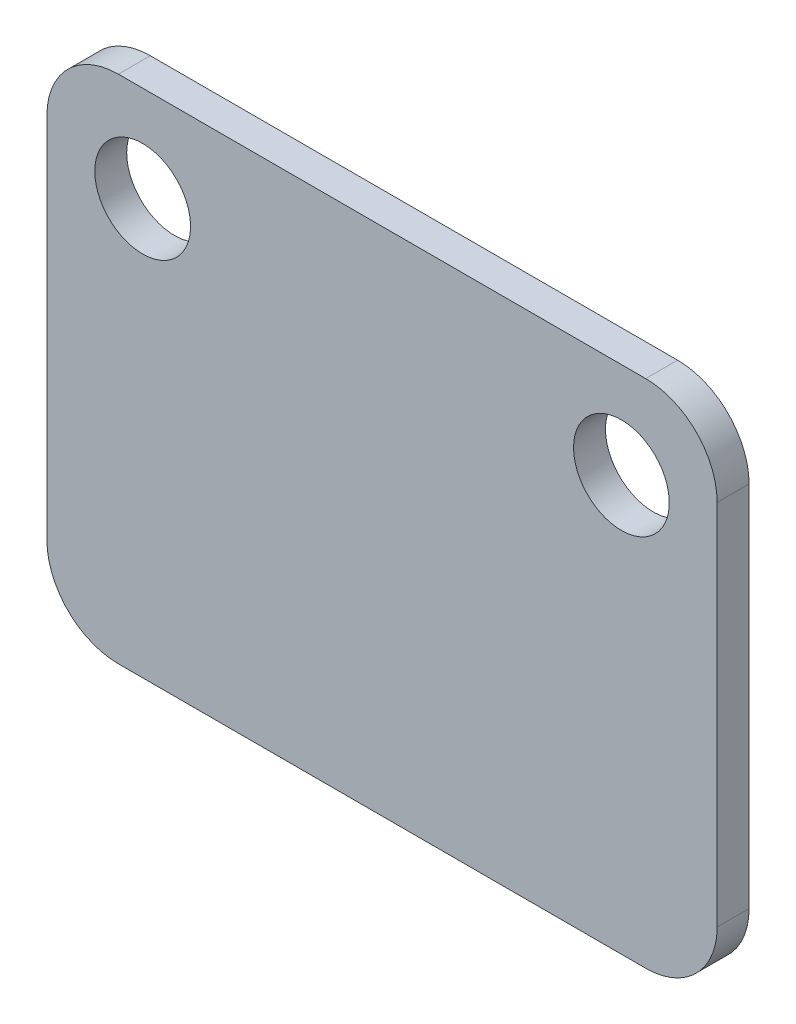
SolidWorks part; units mm, degrees
material "Cobre"
ref_plane "Plano frontal" through (0, 0, 0) normal (0, 0, 1) x (1, 0, 0)
ref_plane "Plano superior" through (0, 0, 0) normal (0, 1, 0) x (1, 0, 0)
ref_plane "Plano direito" through (0, 0, 0) normal (1, 0, 0) x (0, 0, -1)
sketch "Esboço6" plane through (0, 0, 0) normal (0, 0, 1) x (1, 0, 0)
  line L1 (71.3519, 949.0564) -> (54.8319, 949.0564)
  line L2 (73.5919, 946.8164) -> (73.5919, 935.2964)
  line L3 (71.3519, 933.0564) -> (54.8319, 933.0564)
  line L4 (52.5919, 946.8164) -> (52.5919, 935.2964)
  arc A0 (54.8319, 933.0564) -> (52.5919, 935.2964) centre (54.8319, 935.2964) cw
  arc A1 (54.8319, 949.0564) -> (52.5919, 946.8164) centre (54.8319, 946.8164) ccw
  arc A2 (71.3519, 949.0564) -> (73.5919, 946.8164) centre (71.3519, 946.8164) cw
  arc A3 (73.5919, 935.2964) -> (71.3519, 933.0564) centre (71.3519, 935.2964) cw
  dimension "D3" = 2.24
  dimension "D1" = 16
  dimension "D2" = 21
extrude "Ressalto-extrusão2" add sketch "Esboço6" along normal blind 1 contours L2 A3 L3 A0 L4 A1 L1 A2
sketch "Esboço7" plane through (0, 0, 0) normal (0, 0, -1) x (-1, 0, 0)
  line L0 (-73.5919, 946.8164) -> (-73.5919, 935.2964) construction
  line L1 (-52.5919, 946.8164) -> (-52.5919, 935.2964) construction
  line L2 (-71.3519, 949.0564) -> (-54.8319, 949.0564) construction
  circle A0 centre (-55.5919, 946.0564) radius 1.5
  circle A1 centre (-70.5919, 946.0564) radius 1.5
  dimension "D1" = 15
  dimension "D2" = 3
  dimension "D3" = 3
  dimension "D4" = 3
  dimension "D5" = 3
  dimension "D6" = 3
  dimension "D7" = 3
extrude "Corte-extrusão4" cut sketch "Esboço7" against normal blind 3
